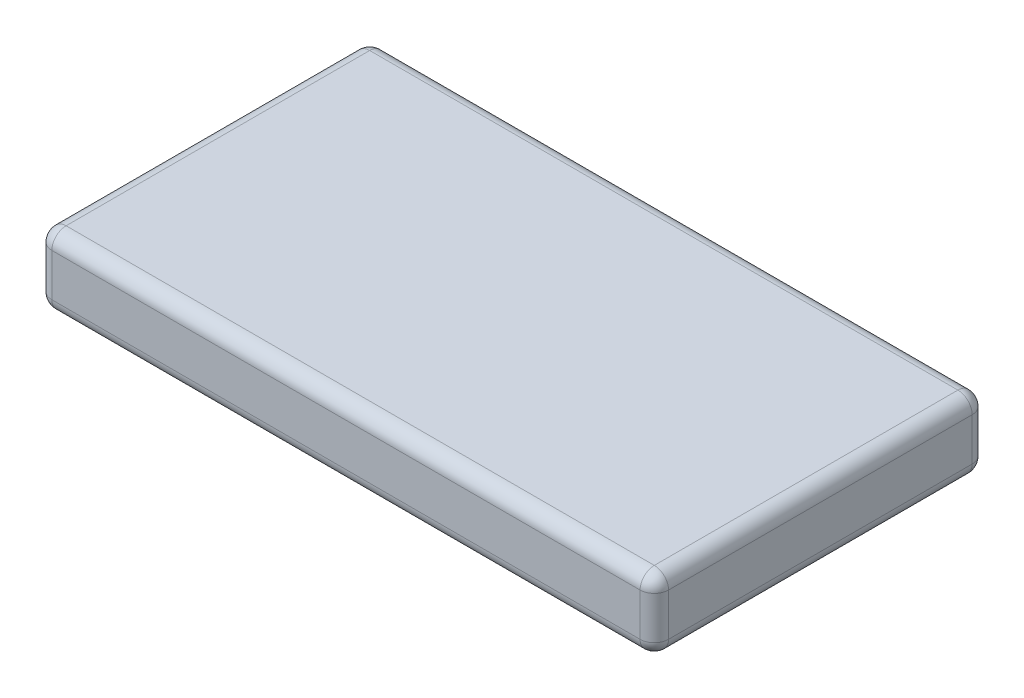
SolidWorks part; units mm, degrees
ref_plane "Front Plane" through (0, 0, 0) normal (0, 0, 1) x (1, 0, 0)
ref_plane "Top Plane" through (0, 0, 0) normal (0, 1, 0) x (1, 0, 0)
ref_plane "Right Plane" through (0, 0, 0) normal (1, 0, 0) x (0, 0, -1)
sketch "Sketch1" plane through (0, 0, 0) normal (0, 1, 0) x (1, 0, 0)
  line L1 (-65, 35) -> (65, 35)
  line L2 (-65, 35) -> (-65, -35)
  line L3 (-65, -35) -> (65, -35)
  line L4 (65, 35) -> (65, -35)
  line L5 (-65, 35) -> (65, -35) construction
  line L6 (-65, -35) -> (65, 35) construction
  point P0 (0, 0)
extrude "Boss-Extrude1" add sketch "Sketch1" along normal blind 15
fillet "Fillet1" radius 3 12 edges at (65, 7.5, 35) (65, 7.5, -35) (-65, 7.5, -35) (-65, 7.5, 35) (0, 0, -35) (-65, 0, 0) (0, 0, 35) (65, 0, 0) (0, 15, 35) (-65, 15, 0) (0, 15, -35) (65, 15, 0)
